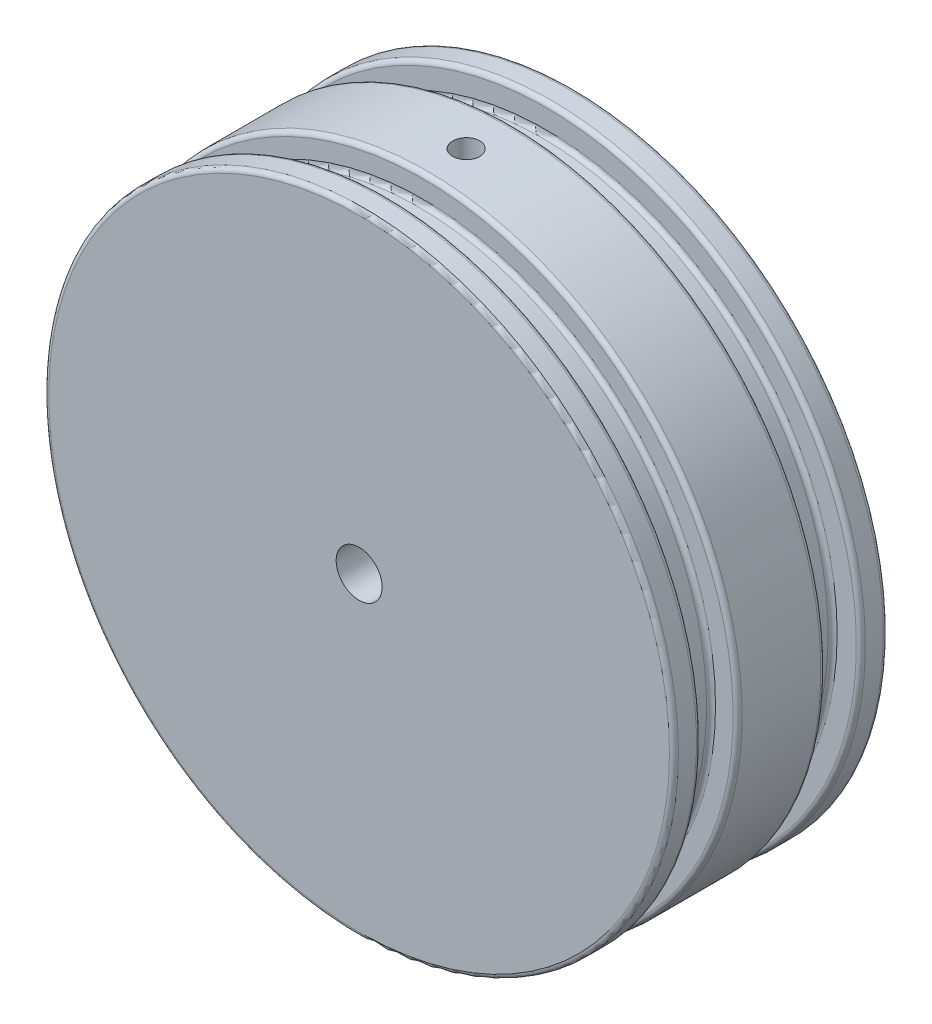
SolidWorks part; units mm, degrees
material "Delrin 2700 NC010, Low Viscosity Acetal Copolymer (SS)"
ref_plane "Front Plane" through (0, 0, 0) normal (0, 0, 1) x (1, 0, 0)
ref_plane "Top Plane" through (0, 0, 0) normal (0, 1, 0) x (1, 0, 0)
ref_plane "Right Plane" through (0, 0, 0) normal (1, 0, 0) x (0, 0, -1)
sketch "Sketch1" plane through (0, 0, 0) normal (0, 0, 1) x (1, 0, 0)
  line L0 (36.3902, 69.9) -> (-42.7961, 69.9) construction
  circle A0 centre (0, 0) radius 69.9
  circle A2 centre (0, 0) radius 40 construction
  point P16 (0, 0)
  dimension "D1" = 139.8
  dimension "D3" = 80
extrude "Boss-Extrude1" add sketch "Sketch1" along normal blind 20
sketch "Sketch8" plane through (0, 0, 0) normal (0, 0, -1) x (-1, 0, 0)
  circle A0 centre (0, 0) radius 69.9
  circle A1 centre (0, 0) radius 69.9 construction
extrude "Boss-Extrude2" add sketch "Sketch8" along normal blind 27.5
sketch "Sketch9" plane through (0, 0, -27.5) normal (0, 0, -1) x (-1, 0, 0)
  circle A0 centre (0, 0) radius 8
  dimension "D1" = 16
sketch "Sketch7" plane through (0, 0, 0) normal (0, 1, 0) x (1, 0, 0)
  line L1 (68.25, -9.935) -> (41.6335, -9.935) construction
  line L2 (69.9, 27.5) -> (69.9, -20) construction
  line L4 (64, -14) -> (64, -5.87)
  line L6 (64, -14) -> (69.9, -14)
  line L7 (0, 0) -> (0, -32.716) construction
  line L9 (69.9, -14) -> (69.9, -5.87)
  line L10 (64, -14) -> (69.9, -14) construction
  line L11 (64, -14) -> (64, -9.935)
  line L14 (64, -5.87) -> (69.9, -5.87)
  line L15 (69.9, 17.565) -> (41.6335, 17.565) construction
  line L16 (63.6352, 13.63) -> (63.6352, 21.5)
  line L17 (63.6352, 13.63) -> (69.9, 13.63)
  line L18 (63.6352, 13.63) -> (69.9, 13.63) construction
  line L19 (69.9, 13.63) -> (69.9, 21.5)
  line L20 (63.6352, 21.5) -> (69.9, 21.5)
  point P12 (62.0905, -9.935)
  point P24 (63.6352, 17.565)
  dimension "D1" = 4.065
  dimension "D2" = 5.9
  dimension "D3" = 0
  dimension "D4" = 6
  dimension "D5" = 6
  dimension "D6" = 3.935
  dimension "D7" = 6.2648
  dimension "D8" = 0
revolve "Cut-Revolve2" cut sketch "Sketch7" angle 360 about L7
fillet "Fillet1" radius 1 10 edges at (-69.9, 0, 14) (-69.9, 0, 5.87) (-64, 0, 5.87) (-64, 0, 14) (-63.6352, 0, -21.5) (-69.9, 0, -21.5) (-69.9, 0, -13.63) (-63.6352, 0, -13.63) (-69.9, 0, -27.5) (69.9, 0, 20)
hole_wizard "M12x1.75 Tapped Hole1" positions "Sketch10" profile "Sketch11" tap size "M12x1.75" standard "ANSI Metric"
sketch "Sketch10" plane through (0, 0, -27.5) normal (0, 0, -1) x (-1, 0, 0)
  point P0 (0, 0)
sketch "Sketch11" plane through (0, 0, -27.5) normal (1, 0, 0) x (0, 1, 0)
  line L0 (0, 0) -> (0, 20.5644)
  line L1 (0, 20.5644) -> (5.1, 17.5)
  line L2 (5.1, 17.5) -> (5.1, 0)
  line L5 (5.1, 0) -> (0, 0)
  line L10 (0, 20.5644) -> (-5.1, 17.5) construction
  line L11 (0, -6.35) -> (0, 107.95) construction
  dimension "Tap Drill Dia." = 10.2
  dimension "Tap Drill Depth" = 17.5
  dimension "Drill Angle" = 118
cosmetic thread "Hole Thread1" parameters "D1"=17.5, "D2"=12
hole_wizard "M12x1.75 Tapped Hole2" positions "Sketch12" profile "Sketch13" tap size "M12x1.75" standard "ANSI Metric"
sketch "Sketch12" plane through (0, 0, 20) normal (0, 0, 1) x (1, 0, 0)
  point P0 (0, 0)
sketch "Sketch13" plane through (0, 0, 20) normal (1, 0, 0) x (0, -1, 0)
  line L0 (0, 0) -> (0, 20.5644)
  line L1 (0, 20.5644) -> (5.1, 17.5)
  line L2 (5.1, 17.5) -> (5.1, 0)
  line L5 (5.1, 0) -> (0, 0)
  line L10 (0, 20.5644) -> (-5.1, 17.5) construction
  line L11 (0, -6.35) -> (0, 107.95) construction
  dimension "Tap Drill Dia." = 10.2
  dimension "Tap Drill Depth" = 17.5
  dimension "Drill Angle" = 118
cosmetic thread "Hole Thread2" parameters "D1"=17.5, "D2"=12
ref_plane "Plane1" through (0, 69.9, 0) normal (0, -1, 0) x (-1, 0, 0)
sketch "Sketch14" plane through (0, 69.9, 0) normal (0, -1, 0) x (-1, 0, 0)
  line L0 (69.9, 26.5) -> (-69.9, 26.5) construction
  line L1 (-69.9, -19) -> (69.9, -19) construction
  line L2 (69.9, 26.5) -> (-69.9, 26.5)
  line L3 (-69.9, -19) -> (69.9, -19)
  line L4 (0, -19) -> (0, 26.5) construction
  circle A0 centre (0, 3.75) radius 3
  dimension "D1" = 6
sketch "Sketch15" plane through (0, 0, -27.5) normal (0, 0, -1) x (-1, 0, 0)
  arc A1 (3, 69.8356) -> (-3, 69.8356) centre (0, 0) ccw construction
  circle A2 centre (0, 42.9) radius 3
  point P5 (0, 69.9)
  dimension "D2" = 6
  dimension "D1" = 27
hole_wizard "Ø6.0mm Dowel Hole1" positions "Sketch16" profile "Sketch17" hole size "Ø6.0" standard "ANSI Metric"
sketch "Sketch16" plane through (0, 69.9, 0) normal (0, -1, 0) x (-1, 0, 0)
  point P0 (0, 3.75)
sketch "Sketch17" plane through (0, 69.9, -3.75) normal (1, 0, 0) x (0, 0, 1)
  line L0 (0, 0) -> (0, 28.8026)
  line L1 (0, 28.8026) -> (3, 27)
  line L2 (3, 27) -> (3, 0)
  line L5 (3, 0) -> (0, 0)
  line L10 (0, 28.8026) -> (-3, 27) construction
  line L11 (0, -6.35) -> (0, 107.95) construction
  dimension "Hole Dia." = 6
  dimension "Hole Depth" = 27
  dimension "Drill Angle" = 118
hole_wizard "Ø6.0mm Dowel Hole2" positions "Sketch18" profile "Sketch19" hole size "Ø6.0" standard "ANSI Metric"
sketch "Sketch18" plane through (0, 0, -27.5) normal (0, 0, -1) x (-1, 0, 0)
  point P0 (0, 42.9)
sketch "Sketch19" plane through (0, 42.9, -27.5) normal (1, 0, 0) x (0, 1, 0)
  line L0 (0, 0) -> (0, 25.5526)
  line L1 (0, 25.5526) -> (3, 23.75)
  line L2 (3, 23.75) -> (3, 0)
  line L5 (3, 0) -> (0, 0)
  line L10 (0, 25.5526) -> (-3, 23.75) construction
  line L11 (0, -6.35) -> (0, 107.95) construction
  dimension "Hole Dia." = 6
  dimension "Hole Depth" = 23.75
  dimension "Drill Angle" = 118
